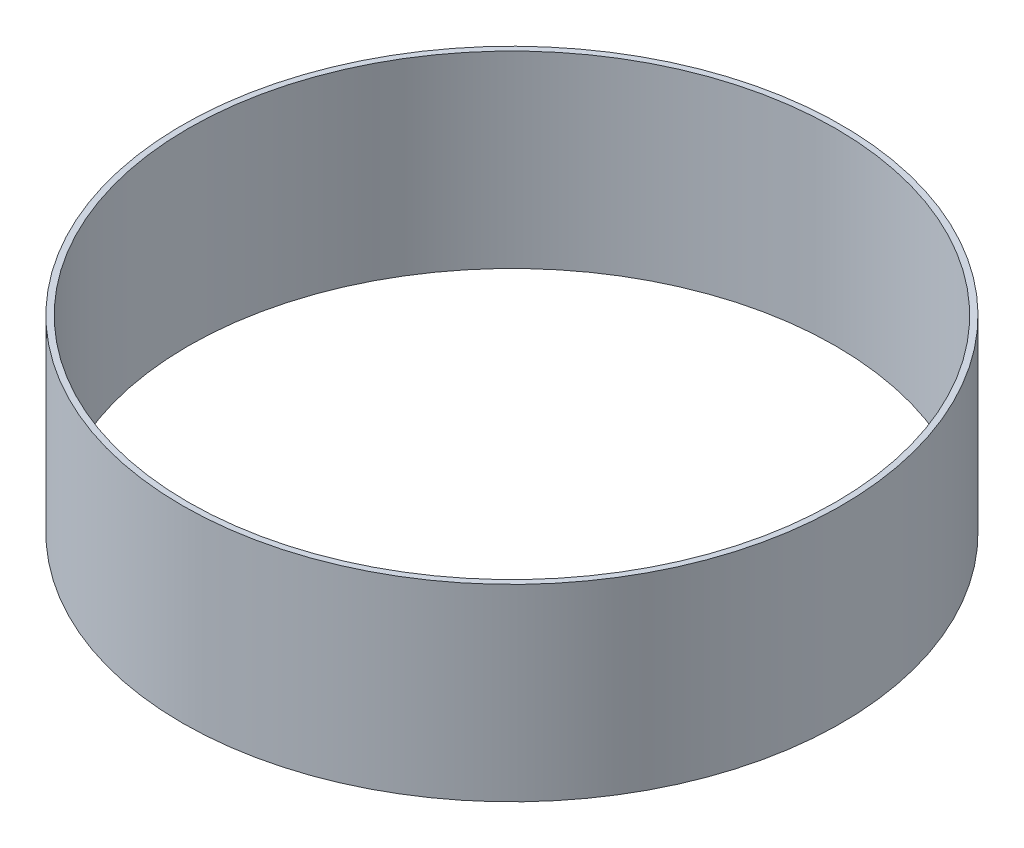
SolidWorks part; units mm, degrees
ref_plane "Front Plane" through (0, 0, 0) normal (0, 0, 1) x (1, 0, 0)
ref_plane "Top Plane" through (0, 0, 0) normal (0, 1, 0) x (1, 0, 0)
ref_plane "Right Plane" through (0, 0, 0) normal (1, 0, 0) x (0, 0, -1)
sketch "Sketch1" plane through (0, 0, 0) normal (0, 1, 0) x (1, 0, 0)
  circle A0 centre (0, 0) radius 177.8
  circle A1 centre (0, 0) radius 174.625
  dimension "D1" = 355.6
  dimension "D2" = 3.175
extrude "Boss-Extrude1" add sketch "Sketch1" along normal blind 101.6
